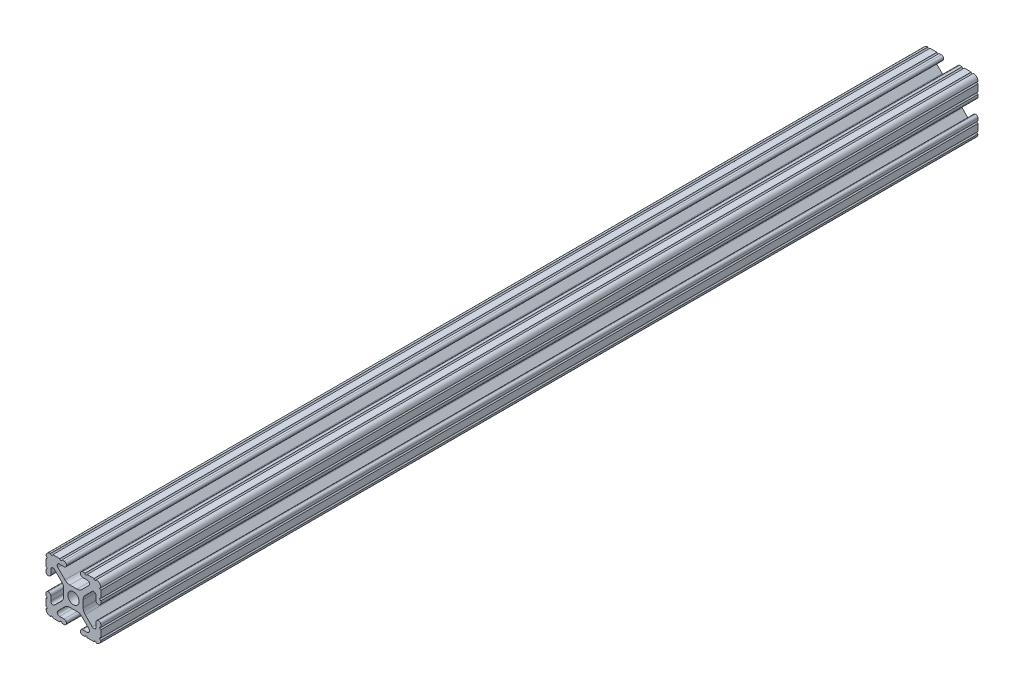
SolidWorks part; units mm, degrees
material "6105-t5"
ref_plane "Front Plane" through (0, 0, 0) normal (0, 0, 1) x (1, 0, 0)
ref_plane "Top Plane" through (0, 0, 0) normal (0, 1, 0) x (1, 0, 0)
ref_plane "Right Plane" through (0, 0, 0) normal (1, 0, 0) x (0, 0, -1)
sketch "Sketch1" plane through (0, 0, 0) normal (0, 0, 1) x (1, 0, 0)
  line L0 (-7.207, 8.7244) -> (-3.8983, 5.4232)
  line L1 (-4.2875, 10.4902) -> (-6.4768, 10.4902)
  line L2 (-3.2385, 11.651) -> (-3.2385, 11.5392)
  line L3 (-5.3171, 12.7) -> (-4.2875, 12.7)
  line L4 (0, 13.4005) -> (0, -14.8534) construction
  line L5 (12.7, 0) -> (-13.9989, 0) construction
  line L6 (-9.5504, 12.7) -> (-6.3331, 12.7)
  line L7 (-12.7, 6.3331) -> (-12.7, 9.5504)
  line L8 (-12.7, 4.2875) -> (-12.7, 5.3171)
  line L9 (-11.5392, 3.2385) -> (-11.651, 3.2385)
  line L10 (-10.4902, 6.4021) -> (-10.4902, 4.2875)
  line L11 (-5.441, 3.8408) -> (-8.7371, 7.1294)
  line L12 (-4.5085, -1.5932) -> (-4.5085, 1.5932)
  line L13 (-1.7093, -4.4958) -> (1.7093, -4.4958)
  line L14 (3.9523, -5.4237) -> (7.1797, -8.6452)
  line L15 (6.4164, -10.4902) -> (4.2875, -10.4902)
  line L16 (3.2385, -11.5392) -> (3.2385, -11.651)
  line L17 (4.2875, -12.7) -> (5.3171, -12.7)
  line L18 (6.3331, -12.7) -> (9.5504, -12.7)
  line L19 (12.7, -9.5504) -> (12.7, -6.3331)
  line L20 (12.7, -5.3171) -> (12.7, -4.2875)
  line L21 (11.651, -3.2385) -> (11.5392, -3.2385)
  line L22 (10.4902, -4.2875) -> (10.4902, -6.4021)
  line L23 (8.7371, -7.1294) -> (5.441, -3.8408)
  line L24 (4.5085, -1.5932) -> (4.5085, 1.5932)
  line L25 (5.441, 3.8408) -> (8.7371, 7.1294)
  line L26 (10.4902, 6.4021) -> (10.4902, 4.2875)
  line L27 (11.5392, 3.2385) -> (11.651, 3.2385)
  line L28 (12.7, 4.2875) -> (12.7, 5.3171)
  line L29 (12.7, 6.3331) -> (12.7, 9.5504)
  line L30 (9.5504, 12.7) -> (6.3331, 12.7)
  line L31 (5.3171, 12.7) -> (4.2875, 12.7)
  line L32 (3.2385, 11.651) -> (3.2385, 11.5392)
  line L33 (4.2875, 10.4902) -> (6.4768, 10.4902)
  line L34 (7.207, 8.7244) -> (3.8983, 5.4232)
  line L35 (1.6558, 4.4958) -> (-1.6558, 4.4958)
  line L36 (-8.7371, -7.1294) -> (-5.441, -3.8408)
  line L37 (-10.4902, -4.2875) -> (-10.4902, -6.4021)
  line L38 (-11.651, -3.2385) -> (-11.5392, -3.2385)
  line L39 (-12.7, -5.3171) -> (-12.7, -4.2875)
  line L40 (-12.7, -9.5504) -> (-12.7, -6.3331)
  line L41 (-6.3331, -12.7) -> (-9.5504, -12.7)
  line L42 (-4.2875, -12.7) -> (-5.3171, -12.7)
  line L43 (-3.2385, -11.5392) -> (-3.2385, -11.651)
  line L44 (-6.4164, -10.4902) -> (-4.2875, -10.4902)
  line L45 (-3.9523, -5.4237) -> (-7.1797, -8.6452)
  arc A0 (-7.207, 8.7244) -> (-6.4768, 10.4902) centre (-6.4768, 9.4563) cw
  arc A1 (-3.2385, 11.5392) -> (-4.2875, 10.4902) centre (-4.2875, 11.5392) cw
  arc A2 (-4.2875, 12.7) -> (-3.2385, 11.651) centre (-4.2875, 11.651) cw
  arc A3 (-5.3171, 12.7) -> (-6.3331, 12.7) centre (-5.8251, 12.7) cw
  arc A4 (-9.5504, 12.7) -> (-10.5664, 12.6998) centre (-10.0584, 12.7) cw
  arc A5 (-12.6998, 10.5664) -> (-10.5664, 12.6998) centre (-10.5918, 10.5918) cw
  arc A6 (-12.6998, 10.5664) -> (-12.7, 9.5504) centre (-12.7, 10.0584) cw
  arc A7 (-12.7, 6.3331) -> (-12.7, 5.3171) centre (-12.7, 5.8251) cw
  arc A8 (-11.651, 3.2385) -> (-12.7, 4.2875) centre (-11.651, 4.2875) cw
  arc A9 (-10.4902, 4.2875) -> (-11.5392, 3.2385) centre (-11.5392, 4.2875) cw
  circle A10 centre (0, 0) radius 2.6035
  arc A11 (-10.4902, 6.4021) -> (-8.7371, 7.1294) centre (-9.4628, 6.4021) cw
  arc A12 (-5.441, 3.8408) -> (-4.5085, 1.5932) centre (-7.6835, 1.5932) cw
  arc A13 (-4.5085, -1.5932) -> (-5.441, -3.8408) centre (-7.6835, -1.5932) cw
  arc A14 (-8.7371, -7.1294) -> (-10.4902, -6.4021) centre (-9.4628, -6.4021) cw
  arc A15 (-1.7093, -4.4958) -> (-3.9523, -5.4237) centre (-1.7093, -7.6708) ccw
  arc A16 (3.9523, -5.4237) -> (1.7093, -4.4958) centre (1.7093, -7.6708) ccw
  arc A17 (6.4164, -10.4902) -> (7.1797, -8.6452) centre (6.4164, -9.4098) ccw
  arc A18 (4.2875, -10.4902) -> (3.2385, -11.5392) centre (4.2875, -11.5392) ccw
  arc A19 (3.2385, -11.651) -> (4.2875, -12.7) centre (4.2875, -11.651) ccw
  arc A20 (6.3331, -12.7) -> (5.3171, -12.7) centre (5.8251, -12.7) ccw
  arc A21 (10.5664, -12.6998) -> (9.5504, -12.7) centre (10.0584, -12.7) ccw
  arc A22 (10.5664, -12.6998) -> (12.6998, -10.5664) centre (10.5918, -10.5918) ccw
  arc A23 (12.7, -9.5504) -> (12.6998, -10.5664) centre (12.7, -10.0584) ccw
  arc A24 (12.7, -5.3171) -> (12.7, -6.3331) centre (12.7, -5.8251) ccw
  arc A25 (12.7, -4.2875) -> (11.651, -3.2385) centre (11.651, -4.2875) ccw
  arc A26 (11.5392, -3.2385) -> (10.4902, -4.2875) centre (11.5392, -4.2875) ccw
  arc A27 (8.7371, -7.1294) -> (10.4902, -6.4021) centre (9.4628, -6.4021) ccw
  arc A28 (4.5085, -1.5932) -> (5.441, -3.8408) centre (7.6835, -1.5932) ccw
  arc A29 (5.441, 3.8408) -> (4.5085, 1.5932) centre (7.6835, 1.5932) ccw
  arc A30 (10.4902, 6.4021) -> (8.7371, 7.1294) centre (9.4628, 6.4021) ccw
  arc A31 (10.4902, 4.2875) -> (11.5392, 3.2385) centre (11.5392, 4.2875) ccw
  arc A32 (11.651, 3.2385) -> (12.7, 4.2875) centre (11.651, 4.2875) ccw
  arc A33 (12.7, 6.3331) -> (12.7, 5.3171) centre (12.7, 5.8251) ccw
  arc A34 (12.6998, 10.5664) -> (12.7, 9.5504) centre (12.7, 10.0584) ccw
  arc A35 (12.6998, 10.5664) -> (10.5664, 12.6998) centre (10.5918, 10.5918) ccw
  arc A36 (9.5504, 12.7) -> (10.5664, 12.6998) centre (10.0584, 12.7) ccw
  arc A37 (5.3171, 12.7) -> (6.3331, 12.7) centre (5.8251, 12.7) ccw
  arc A38 (4.2875, 12.7) -> (3.2385, 11.651) centre (4.2875, 11.651) ccw
  arc A39 (3.2385, 11.5392) -> (4.2875, 10.4902) centre (4.2875, 11.5392) ccw
  arc A40 (7.207, 8.7244) -> (6.4768, 10.4902) centre (6.4768, 9.4563) ccw
  arc A41 (1.6558, 4.4958) -> (3.8983, 5.4232) centre (1.6558, 7.6708) ccw
  arc A42 (-1.6558, 4.4958) -> (-3.8983, 5.4232) centre (-1.6558, 7.6708) cw
  arc A43 (-11.5392, -3.2385) -> (-10.4902, -4.2875) centre (-11.5392, -4.2875) cw
  arc A44 (-12.7, -4.2875) -> (-11.651, -3.2385) centre (-11.651, -4.2875) cw
  arc A45 (-12.7, -5.3171) -> (-12.7, -6.3331) centre (-12.7, -5.8251) cw
  arc A46 (-12.7, -9.5504) -> (-12.6998, -10.5664) centre (-12.7, -10.0584) cw
  arc A47 (-10.5664, -12.6998) -> (-12.6998, -10.5664) centre (-10.5918, -10.5918) cw
  arc A48 (-10.5664, -12.6998) -> (-9.5504, -12.7) centre (-10.0584, -12.7) cw
  arc A49 (-6.3331, -12.7) -> (-5.3171, -12.7) centre (-5.8251, -12.7) cw
  arc A50 (-3.2385, -11.651) -> (-4.2875, -12.7) centre (-4.2875, -11.651) cw
  arc A51 (-4.2875, -10.4902) -> (-3.2385, -11.5392) centre (-4.2875, -11.5392) cw
  arc A52 (-6.4164, -10.4902) -> (-7.1797, -8.6452) centre (-6.4164, -9.4098) cw
  dimension "D1" = 5.207
  dimension "D9" = 14.859
  dimension "D2" = 25.4
  dimension "D3" = 12.7
  dimension "D4" = 6.477
  dimension "D5" = 8.2042
  dimension "D6" = 9.017
  dimension "D8" = 2.2098
  dimension "D10" = 2.2098
extrude "Extrude1" add sketch "Sketch1" against normal blind 406.4
ref_plane "Plane1" through (-5.3171, 565.15, 127) normal (0, 0.9553, 0.2958) x (1, 0, 0)
sketch "Sketch2" plane through (0, -12.7, 0) normal (0, -1, 0) x (1, 0, 0)
  line L0 (-12.7, -406.4) -> (12.7, -406.4)
  line L1 (12.7, -406.4) -> (12.7, -274.574)
  line L2 (12.7, -274.574) -> (-12.7, -266.7114)
  line L3 (-12.7, -266.7114) -> (-12.7, -406.4)
  line L4 (-9.5504, -406.4) -> (-6.3331, -406.4) construction
  line L5 (-9.5504, 0) -> (-6.3331, 0) construction
  line L6 (12.7, -406.4) -> (12.7, 0) construction
  line L7 (-12.7, -406.4) -> (-12.7, 0) construction
  dimension "D1" = 17.2
  dimension "D2" = 0
  dimension "D3" = 274.574
  dimension "D4" = 0
  dimension "D5" = 0
extrude "Cut-Extrude1" [suppressed] cut sketch "Sketch2" against normal through all
